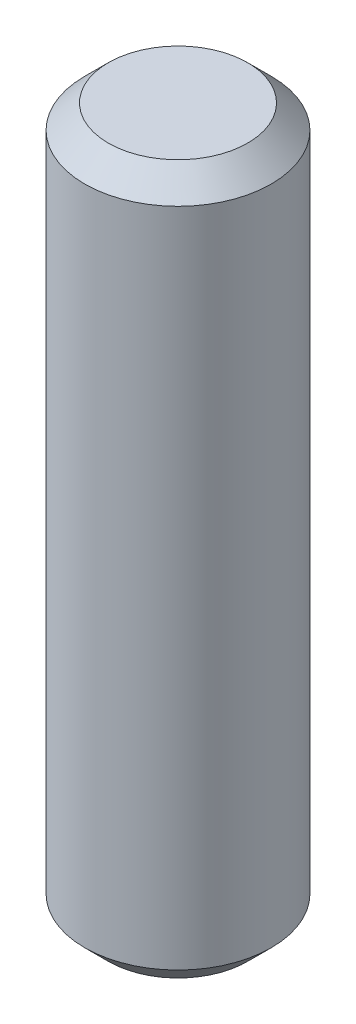
SolidWorks part; units mm, degrees
ref_plane "Front Plane" through (0, 0, 0) normal (0, 0, 1) x (1, 0, 0)
ref_plane "Top Plane" through (0, 0, 0) normal (0, 1, 0) x (1, 0, 0)
ref_plane "Right Plane" through (0, 0, 0) normal (1, 0, 0) x (0, 0, -1)
sketch "Sketch1" plane through (0, 0, 0) normal (0, 1, 0) x (1, 0, 0)
  circle A0 centre (0, 0) radius 3.95
  dimension "D1" = 7.9
extrude "Boss-Extrude1" add sketch "Sketch1" along normal mid plane 30
chamfer "Chamfer1" distance 1 angle 45 2 edges at (0, -15, 3.95) (0, 15, 3.95)
